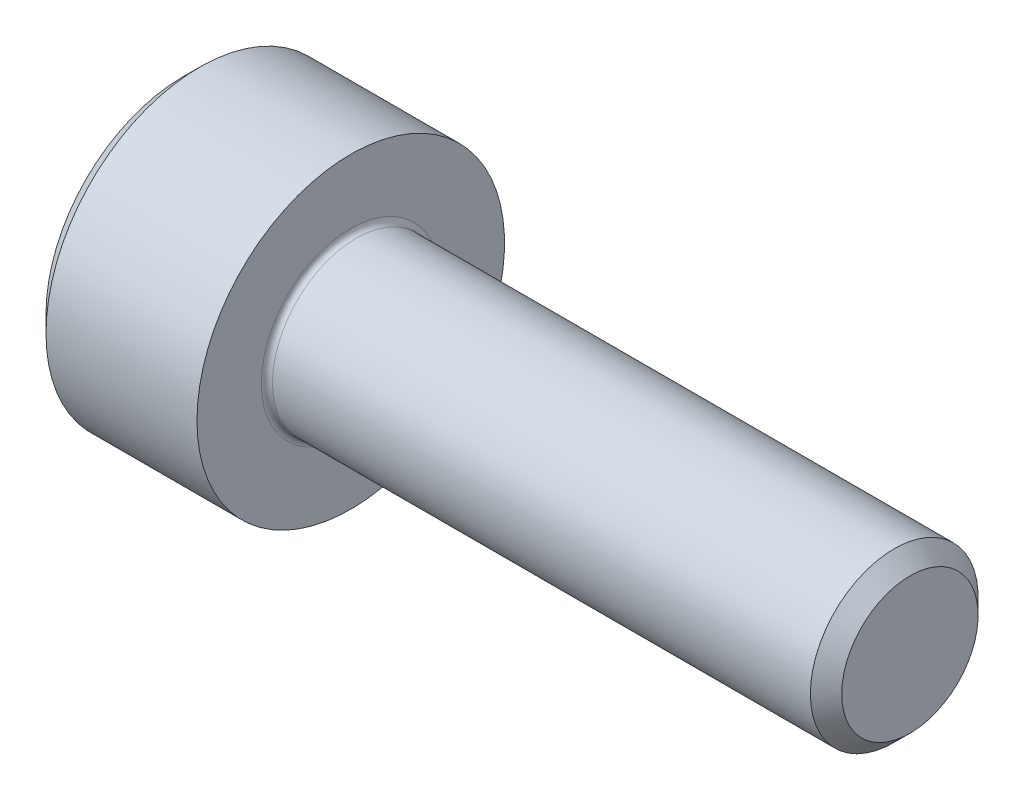
SolidWorks part; units mm, degrees
ref_plane "Plane1" through (0, 0, 0) normal (0, 0, 1) x (1, 0, 0)
ref_plane "Plane2" through (0, 0, 0) normal (0, 1, 0) x (1, 0, 0)
ref_plane "Plane3" through (0, 0, 0) normal (1, 0, 0) x (0, 0, -1)
sketch "BodySke" plane through (0, 0, 0) normal (0, 0, 1) x (1, 0, 0)
  line L0 (0, 0) -> (0, 2.45)
  line L1 (0.3, 2.75) -> (3, 2.75)
  line L2 (3, 2.75) -> (3, 1.5)
  line L3 (3, 1.5) -> (12.7195, 1.5)
  line L4 (13, 1.2195) -> (13, 0)
  line L5 (13, 0) -> (0, 0)
  line L6 (-31.75, 0) -> (127, 0) construction
  line L7 (0, 2.45) -> (0.3, 2.75)
  line L8 (13, 1.2195) -> (12.7195, 1.5)
  line L9 (0, -2.45) -> (0.3, -2.75) construction
  line L10 (13, -1.2195) -> (12.7195, -1.5) construction
  line L11 (3.5, 9.525) -> (3.5, 3.175) construction
  line L12 (3, 9.525) -> (3, 3.175) construction
  line L13 (-37, 9.525) -> (-37, 3.175) construction
  dimension "Diameter" = 3
  dimension "Head_ht" = 3
  dimension "Length" = 10
  dimension "Body_ch_ang" = 45
  dimension "Head_dia" = 5.5
  dimension "Head_ch_ang" = 45
  dimension "Minor_dia" = 2.439
  dimension "Advance" = 0.5
  dimension "Thread_nom" = 10
  dimension "Thread_length" = 50
  dimension "Head_ch_ht" = 0.3
revolve "Base-Revolve" add sketch "BodySke"
cosmetic thread "ThreadCosmetic" [suppressed]
fillet "Fillet1" radius 0.1 1 edges at (3, 0, 1.5)
sketch "Sketch2" plane through (0, 0, 0) normal (0, 0, 1) x (1, 0, 0)
  line L0 (0, 1.28) -> (1.3, 1.28)
  line L1 (1.3, 1.28) -> (2.039, 0)
  line L2 (-31.75, 0) -> (127, 0) construction
  line L3 (2.039, 0) -> (0, 0)
  line L4 (0, 0) -> (0, 1.28)
  line L5 (0, 2.45) -> (0, -2.45) construction
  line L6 (0, 0) -> (47.625, 0) construction
  line L7 (3, -2.75) -> (3, 2.75) construction
  dimension "D1" = 1.28
  dimension "D2" = 60
  dimension "Wall_thickness" = 1.7
revolve "Hex-PreBroach" cut sketch "Sketch2" angle 360 about L6
sketch "Sketch3" plane through (0, 0, 0) normal (-1, 0, 0) x (0, 0.5, 0.866)
  line L0 (0.739, 1.28) -> (-0.739, 1.28)
  line L1 (-0.739, 1.28) -> (-1.478, 0)
  line L2 (0.739, 1.28) -> (1.478, 0)
  line L3 (0.739, -1.28) -> (1.478, 0)
  line L4 (0.739, -1.28) -> (-0.739, -1.28)
  line L5 (-0.739, -1.28) -> (-1.478, 0)
  dimension "D1" = 1.28
  dimension "D2" = 1.28
  dimension "Hex_size" = 2.56
extrude "Hex" cut sketch "Sketch3" against normal blind 1.3
sketch "Sketch4" [suppressed] plane through (0, 0, 0) normal (-1, 0, 0) x (0, 0, 1)
  line L0 (0, 0) -> (10.1727, 0)
  line L1 (0, 0) -> (6.1484, 3.5498) construction
  line L2 (0, 0) -> (5.0863, 8.8098)
  line L3 (8.4417, 2.1022) -> (9.7612, 2.864)
  line L4 (6.0414, 6.2596) -> (7.3609, 7.0215)
  arc A0 (8.4417, 2.1022) -> (6.0414, 6.2596) centre (0, 0) ccw
  arc A1 (10.1727, 0) -> (9.7612, 2.864) centre (0, 0) ccw
  arc A2 (5.0863, 8.8098) -> (7.3609, 7.0215) centre (0, 0) cw
  dimension "D1" = 30
  dimension "Spline_n_dim" = 2.4892
  dimension "Spline_m_dim" = 2.921
  dimension "D2" = 60
  dimension "D3" = 0.3175
  dimension "Spline_p_dim" = 0.635
extrude "Spline" [suppressed] cut sketch "Sketch4" against normal blind 1.3
pattern_circular "CirPattern1" [suppressed] count 6 every 60
sketch "Sketch5" [suppressed] plane through (0, 0, 0) normal (0, 0, 1) x (1, 0, 0)
  line L0 (-31.75, 0) -> (127, 0) construction
  line L2 (0, 15.6) -> (0, -15.6) construction
  circle A0 centre (7.3, 0) radius 1.075
  dimension "Drilled_hole_dia" = 0.95
  dimension "Drilled_hole_loc" = 1.2
extrude "Hole" [suppressed] cut sketch "Sketch5" against normal through all and the other way through all
pattern_circular "Drilled-4" [suppressed] count 2 every 60
pattern_circular "Drilled-6" [suppressed] count 3 every 60
sketch "ThdSchSke" [suppressed] plane through (0, 0, 0) normal (0, 0, 1) x (1, 0, 0)
  line L0 (3.5, -1.2195) -> (3.3036, -1.5)
  line L1 (3.5, -1.2195) -> (3.6964, -1.5)
  line L2 (3.6964, -1.5) -> (3.6964, -1.875)
  line L3 (-3.175, 0) -> (5.1513, 0) construction
  line L5 (3.6964, -1.875) -> (3.3036, -1.875)
  line L6 (3.3036, -1.875) -> (3.3036, -1.5)
  line L7 (0, 2.45) -> (0, -2.45) construction
  dimension "Thread_minor" = 2.439
  dimension "Diameter" = 3
  dimension "Start" = 3.5
  dimension "SideAngle" = 55
  dimension "VeeAngle" = 70
  dimension "Overcut" = 3.75
revolve "ThreadSchematic" [suppressed] cut sketch "ThdSchSke" angle 360 about L3
pattern_linear "ThdSchPat" [suppressed]
equation "\"D2@Sketch3\" = \"Hex_size@Sketch3\" / 2"
equation "\"D1@Sketch3\" = \"Hex_size@Sketch3\" / 2"
equation "\"D1@Sketch2\" = \"Hex_size@Sketch3\" / 2"
equation "\"D3@Sketch4\" = \"Spline_p_dim@Sketch4\" / 2"
equation "\"Thread_minor@ThreadCosmetic\"  =  \"Minor_dia@BodySke\""
equation "\"D2@CirPattern1\" = 360 / \"Num_teeth@CirPattern1\""
equation "\"Wall_thickness@Sketch2\" = \"Head_ht@BodySke\" - \"Key_eng@Hex\""
equation "\"Thread_length@ThreadCosmetic\" = ((sgn( (\"Length@BodySke\" - \"Advance@BodySke\" ) - \"Thread_nom@BodySke\" )-1)*( (\"Length@BodySke\" - \"Advance@BodySke\" ) - \"Thread_nom@BodySke\" ))/-2+ \"Thread_nom@BodySke\""
equation "\"Thread_minor@ThdSchSke\" = \"Minor_dia@BodySke\""
equation "\"Diameter@ThdSchSke\" = \"Diameter@BodySke\""
equation "\"Overcut@ThdSchSke\" = \"Diameter@BodySke\" * 1.25"
equation "\"Start@ThdSchSke\" = \"Head_ht@BodySke\" + \"Length@BodySke\" - \"Thread_length@ThreadCosmetic\"  '---Non-countersunk---"
equation "\"Num_threads@ThdSchPat\" = int( \"Thread_length@ThreadCosmetic\" / \"Advance@BodySke\" + 0.999 )  + 1"
equation "\"Advance@ThdSchPat\" = \"Thread_length@ThreadCosmetic\" /  (\"Num_threads@ThdSchPat\" - 1) 'relax it"
equation "\"Num_threads@ThdSchPat\" = \"Num_threads@ThdSchPat\" - sgn( \"Num_threads@ThdSchPat\" - 1) '---chamfered tips only---"
